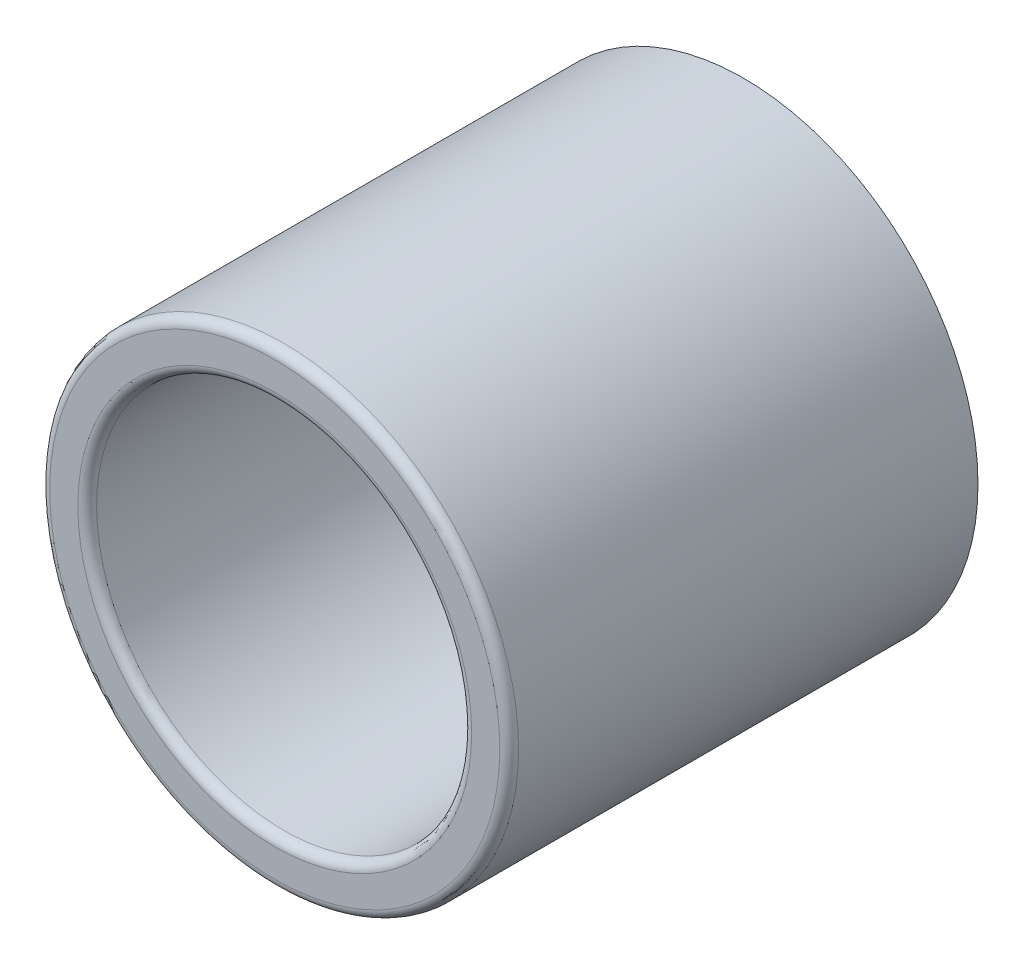
SolidWorks part; units mm, degrees
ref_plane "Front Plane" through (0, 0, 0) normal (0, 0, 1) x (1, 0, 0)
ref_plane "Top Plane" through (0, 0, 0) normal (0, 1, 0) x (1, 0, 0)
ref_plane "Right Plane" through (0, 0, 0) normal (1, 0, 0) x (0, 0, -1)
sketch "Sketch1" plane through (0, 0, 0) normal (0, 0, 1) x (1, 0, 0)
  circle A0 centre (0, 0) radius 2.5
  circle A1 centre (0, 0) radius 2
  dimension "D1" = 5
  dimension "D2" = 4
extrude "Boss-Extrude1" add sketch "Sketch1" along normal blind 5
fillet "Fillet1" radius 0.1 2 edges at (2, 0, 5) (2.5, 0, 5)
